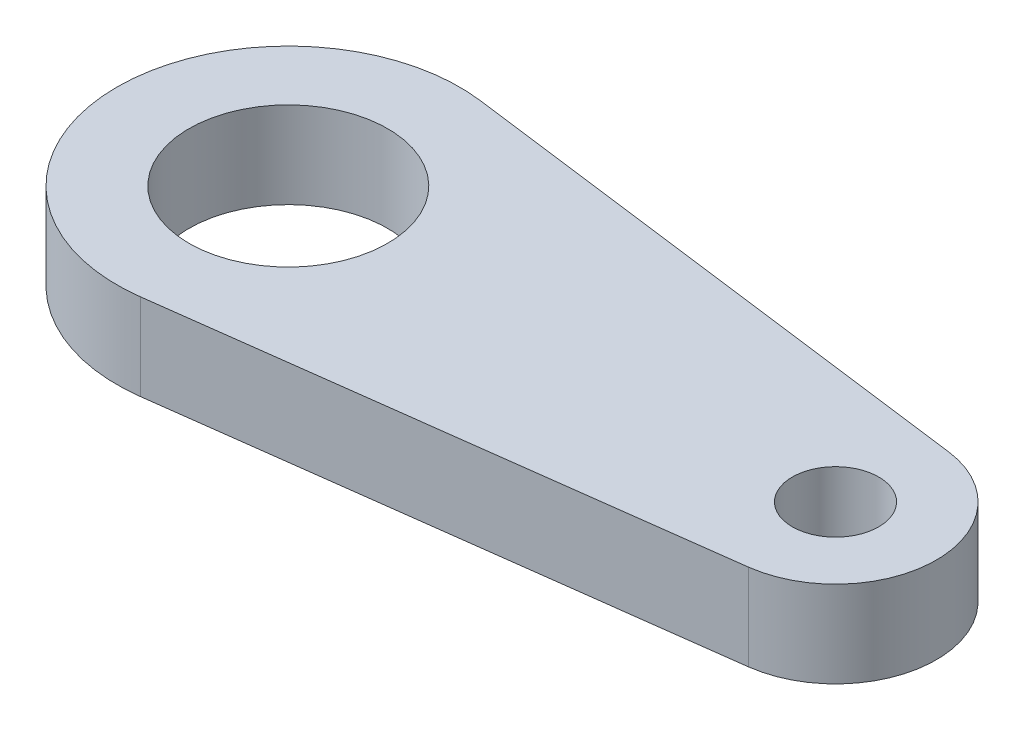
SolidWorks part; units mm, degrees
material "Acrylic (Medium-high impact)"
ref_plane "Plano frontal" through (0, 0, 0) normal (0, 0, 1) x (1, 0, 0)
ref_plane "Plano superior" through (0, 0, 0) normal (0, 1, 0) x (1, 0, 0)
ref_plane "Plano direito" through (0, 0, 0) normal (1, 0, 0) x (0, 0, -1)
sketch "Sketch1" plane through (0, 0, 0) normal (0, 1, 0) x (1, 0, 0)
  line L0 (19.4513, 3.4708) -> (0.7672, 5.9003)
  line L1 (-1.65, 0) -> (1.65, 0) construction
  line L2 (19.4513, -3.4708) -> (0.7672, -5.9003)
  arc A1 (0.7672, 5.9003) -> (0.7672, -5.9003) centre (0, 0) ccw
  arc A2 (19.4513, -3.4708) -> (19.4513, 3.4708) centre (19, 0) ccw
  circle A3 centre (19, 0) radius 1.5
  circle A4 centre (0, 0) radius 3.45
  dimension "D1" = 2.5
  dimension "D2" = 19
  dimension "D3" = 3
  dimension "D4" = 6.9
  dimension "D5" = 2
extrude "Boss-Extrude1" add sketch "Sketch1" along normal mid plane 3
